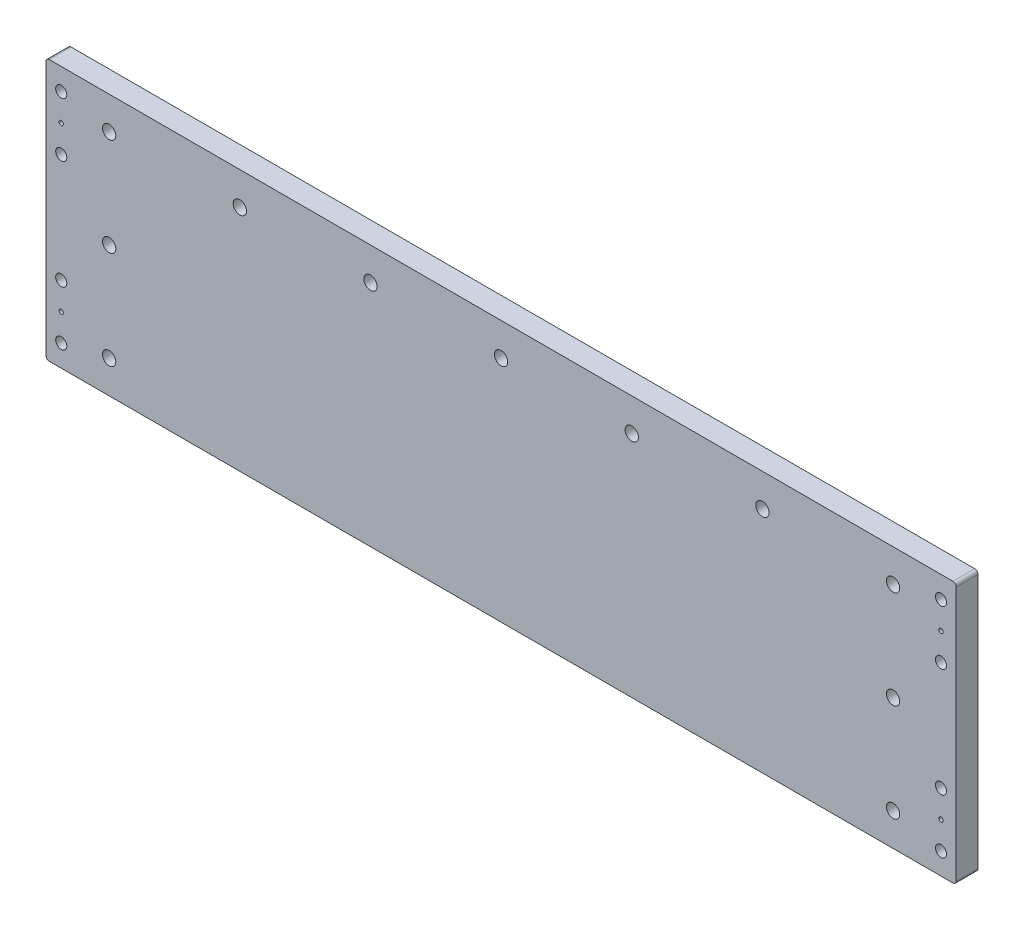
SolidWorks part; units mm, degrees
ref_plane "Front Plane" through (0, 0, 0) normal (0, 0, 1) x (1, 0, 0)
ref_plane "Top Plane" through (0, 0, 0) normal (0, 1, 0) x (1, 0, 0)
ref_plane "Right Plane" through (0, 0, 0) normal (1, 0, 0) x (0, 0, -1)
sketch "Sketch1" plane through (0, 0, 0) normal (0, 0, 1) x (1, 0, 0)
  line L1 (209, -60) -> (-209, -60)
  line L2 (209, -60) -> (209, 60)
  line L3 (209, 60) -> (-209, 60)
  line L4 (-209, -60) -> (-209, 60)
  line L5 (209, -60) -> (-209, 60) construction
  line L6 (209, 60) -> (-209, -60) construction
  point P0 (0, 0)
  dimension "D1" = 418
  dimension "D2" = 120
extrude "Boss-Extrude1" add sketch "Sketch1" along normal mid plane 10
sketch "Sketch3" plane through (0, 0, 5) normal (0, 0, 1) x (1, 0, 0)
  line L0 (-209, 45) -> (209, 45) construction
  line L1 (-209, 60) -> (-209, -60) construction
  line L2 (209, -60) -> (209, 60) construction
  line L3 (-209, -45) -> (209, -45) construction
  line L4 (-180, 60) -> (-180, -60) construction
  line L5 (209, 60) -> (-209, 60) construction
  line L6 (-209, -60) -> (209, -60) construction
  line L7 (180, 60) -> (180, -60) construction
  line L8 (-120, 60) -> (-120, -60) construction
  line L9 (120, 60) -> (120, -60) construction
  line L10 (-1000, 0) -> (49000, 0) construction
  circle A0 centre (-180, 45) radius 3.05
  circle A1 centre (180, 45) radius 3.05
  circle A2 centre (180, -45) radius 3.05
  circle A3 centre (-180, -45) radius 3.05
  circle A4 centre (0, 45) radius 3.05
  circle A5 centre (-120, 45) radius 3.05
  circle A6 centre (120, 45) radius 3.05
  circle A7 centre (-180, 0) radius 3.05
  circle A8 centre (-60, 45) radius 3.05
  circle A9 centre (60, 45) radius 3.05
  circle A10 centre (180, 0) radius 3.05
  dimension "D5" = 6.1
  dimension "D6" = 6.1
  dimension "D7" = 6.1
  dimension "D8" = 6.1
  dimension "D9" = 6.1
  dimension "D12" = 6.1
  dimension "D13" = 6.1
  dimension "D14" = 6.1
  dimension "D11" = 6.1
  dimension "D15" = 6.1
  dimension "D19" = 6.1
  dimension "D1" = 29
  dimension "D2" = 15
  dimension "D3" = 29
  dimension "D4" = 15
  dimension "D10" = 60
  dimension "D16" = 60
  dimension "D17" = 60
  dimension "D18" = 60
extrude "Cut-Extrude2" cut sketch "Sketch3" against normal through all
fillet "Fillet1" radius 1.5 4 edges at (-209, -60, 0) (209, -60, 0) (209, 60, 0) (-209, 60, 0)
sketch "Sketch4" plane through (0, 0, 5) normal (0, 0, 1) x (1, 0, 0)
  line L0 (-202, -1005.069) -> (-202, 48994.931) construction
  line L1 (-209, 58.5) -> (-209, -58.5) construction
  line L2 (207.5, 60) -> (-207.5, 60) construction
  circle A0 centre (-202, 50) radius 2.55
  circle A1 centre (-202, 37.5) radius 1
  circle A2 centre (-202, 25) radius 2.55
  dimension "D2" = 5.1
  dimension "D6" = 5.1
  dimension "D7" = 2
  dimension "D1" = 7
  dimension "D3" = 10
  dimension "D4" = 22.5
  dimension "D5" = 35
extrude "Cut-Extrude3" cut sketch "Sketch4" against normal through all
mirror "Mirror1" about plane through (0, 0, 0) normal (0, 1, 0) of "Cut-Extrude3"
mirror "Mirror2" about plane through (0, 0, 0) normal (1, 0, 0) of "Mirror1", "Cut-Extrude3"
equation "\"D6@Sketch3\"=6.1"
equation "\"D13@Sketch3\"=\"D6@Sketch3\""
equation "\"D9@Sketch3\"=\"D6@Sketch3\""
equation "\"D12@Sketch3\"=\"D6@Sketch3\""
equation "\"D7@Sketch3\"=\"D6@Sketch3\""
equation "\"D5@Sketch3\"=\"D6@Sketch3\""
equation "\"D8@Sketch3\"=\"D6@Sketch3\""
equation "\"D14@Sketch3\"=\"D6@Sketch3\""
equation "\"D1@Sketch3\"=15+14"
equation "\"D3@Sketch3\"=15+14"
equation "\"D11@Sketch3\"=\"D6@Sketch3\""
equation "\"D19@Sketch3\"=\"D6@Sketch3\""
